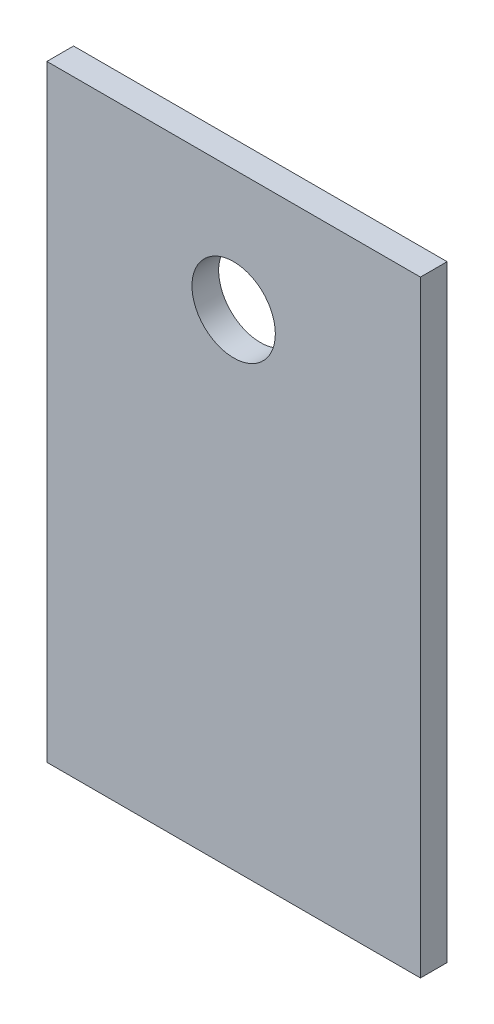
SolidWorks part; units mm, degrees
material "Mahogany"
ref_plane "Front Plane" through (0, 0, 0) normal (0, 0, 1) x (1, 0, 0)
ref_plane "Top Plane" through (0, 0, 0) normal (0, 1, 0) x (1, 0, 0)
ref_plane "Right Plane" through (0, 0, 0) normal (1, 0, 0) x (0, 0, -1)
sketch "Sketch1" plane through (0, 0, 0) normal (0, 0, 1) x (1, 0, 0)
  line L1 (112, -182) -> (-112, -182)
  line L2 (112, -182) -> (112, 182)
  line L3 (112, 182) -> (-112, 182)
  line L4 (-112, -182) -> (-112, 182)
  line L5 (112, -182) -> (-112, 182) construction
  line L6 (112, 182) -> (-112, -182) construction
  point P0 (0, 0)
  dimension "D1" = 224
  dimension "D2" = 364
extrude "Boss-Extrude1" add sketch "Sketch1" along normal blind 16
sketch "Sketch2" plane through (0, 0, 16) normal (0, 0, 1) x (1, 0, 0)
  line L0 (0, 182) -> (0, -182) construction
  line L1 (112, 182) -> (-112, 182) construction
  line L2 (-112, -182) -> (112, -182) construction
  circle A0 centre (0, 109) radius 25
  dimension "D2" = 50
  dimension "D1" = 73
extrude "Cut-Extrude1" cut sketch "Sketch2" against normal through all
